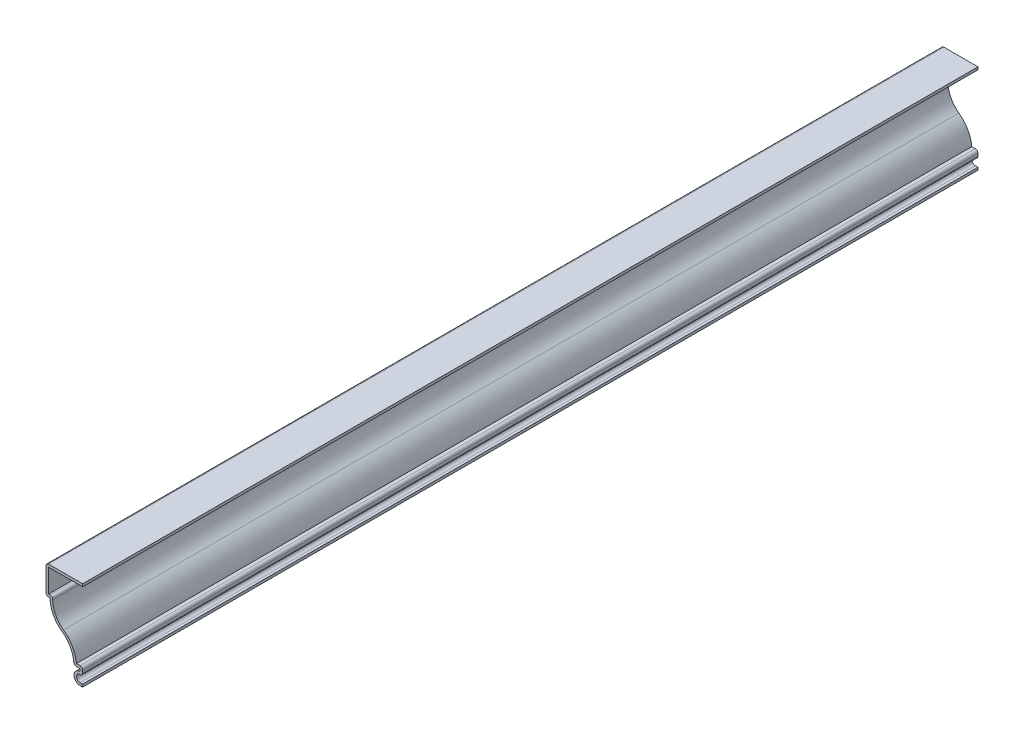
SolidWorks part; units mm, degrees
ref_plane "Front Plane" through (0, 0, 0) normal (0, 0, 1) x (1, 0, 0)
ref_plane "Top Plane" through (0, 0, 0) normal (0, 1, 0) x (1, 0, 0)
ref_plane "Right Plane" through (0, 0, 0) normal (1, 0, 0) x (0, 0, -1)
sketch "Sketch1" plane through (0, 0, 0) normal (0, 0, 1) x (1, 0, 0)
  line L0 (-1.016, 5.7303) -> (-1.016, 4.7625)
  line L1 (-1.016, 5.7303) -> (-3.3973, 5.7303)
  line L2 (-12.7, 23.8125) -> (-14.2875, 23.8125)
  line L3 (-14.2875, 23.8125) -> (-14.2875, 34.925)
  line L4 (-14.2875, 34.925) -> (0, 34.925)
  line L5 (-1.016, 0) -> (0, 0)
  line L6 (-3.3972, 2.3813) -> (-3.3973, 5.7303) construction
  arc A0 (-1.016, 4.7625) -> (-1.016, 0) centre (-1.016, 2.3813) ccw
  arc A1 (-3.3973, 5.7303) -> (-8.0486, 14.7714) centre (-14.5097, 5.7303) ccw
  arc A2 (-8.0486, 14.7714) -> (-12.7, 23.8125) centre (-1.5875, 23.8125) cw
  point P4 (-1.016, 7.984)
  dimension "D3" = 11.1125
  dimension "D4" = 11.1125
  dimension "D1" = 4.7625
  dimension "D2" = 14.2875
  dimension "D5" = 11.1125
  dimension "D6" = 1.5875
  dimension "D7" = 1.016
  dimension "D8" = 34.925
extrude "Extrude-Thin1" add sketch "Sketch1" against normal blind 349.25 thin thin type one direction wall 1.016
fillet "Fillet1" radius 1.016 6 edges at (-3.3973, 5.7303, -174.625) (-11.6328, 24.8285, -174.625) (-14.2875, 23.8125, -174.625) (-14.2875, 34.925, -174.625) (0, 3.2932, -174.625) (0, 6.7463, -174.625)
